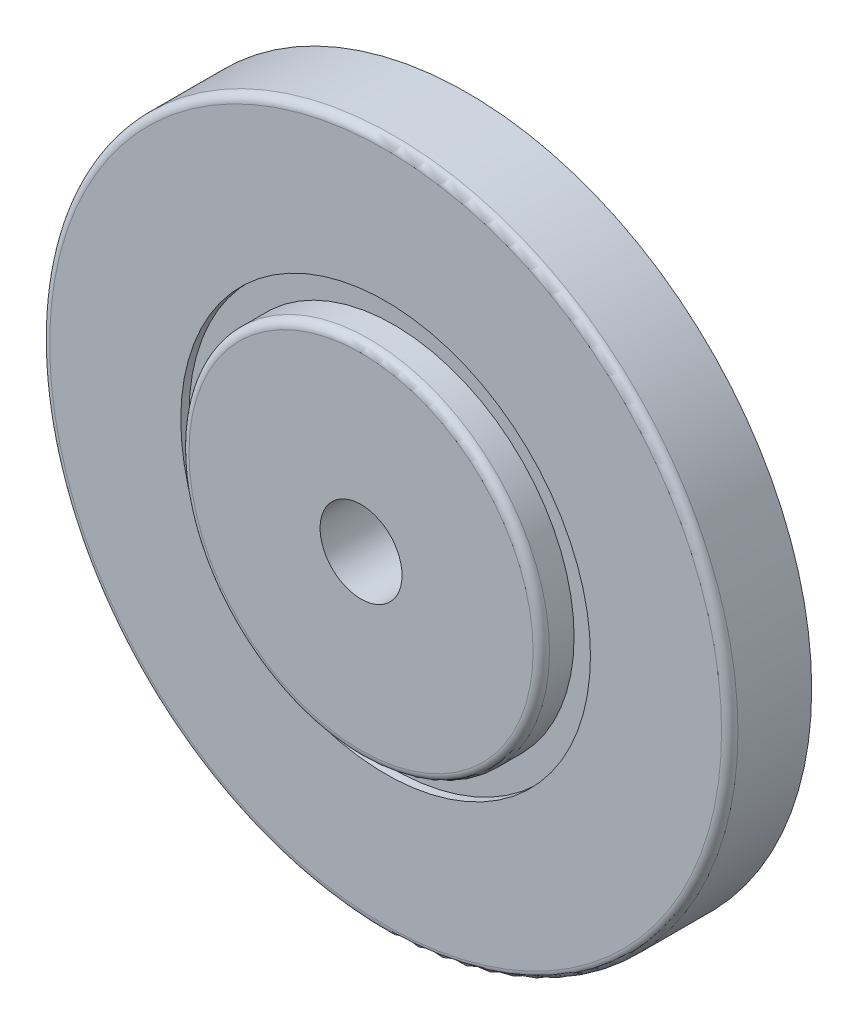
SolidWorks part; units mm, degrees
ref_plane "Alzado" through (0, 0, 0) normal (0, 0, 1) x (1, 0, 0)
ref_plane "Planta" through (0, 0, 0) normal (0, 1, 0) x (1, 0, 0)
ref_plane "Vista lateral" through (0, 0, 0) normal (1, 0, 0) x (0, 0, -1)
sketch "Croquis1" plane through (0, 0, 0) normal (0, 0, 1) x (1, 0, 0)
  circle A0 centre (0, 0) radius 21
  dimension "D1" = 42
extrude "Saliente-Extruir1" add sketch "Croquis1" along normal blind 5
sketch "Croquis2" plane through (0, 0, 5) normal (0, 0, 1) x (1, 0, 0)
  circle A0 centre (0, 0) radius 12.5
  dimension "D1" = 25
extrude "Cortar-Extruir1" cut sketch "Croquis2" against normal blind 0.5
sketch "Croquis3" plane through (0, 0, 4.5) normal (0, 0, 1) x (1, 0, 0)
  circle A0 centre (0, 0) radius 11
  dimension "D1" = 22
extrude "Saliente-Extruir2" add sketch "Croquis3" along normal blind 2
sketch "Croquis4" plane through (0, 0, 6.5) normal (0, 0, 1) x (1, 0, 0)
  circle A0 centre (0, 0) radius 2.5
  dimension "D1" = 5
extrude "Cortar-Extruir2" cut sketch "Croquis4" against normal through all
fillet "Redondeo1" radius 0.5 1 edges at (21, 0, 5)
fillet "Redondeo2" radius 0.5 1 edges at (11, 0, 6.5)
